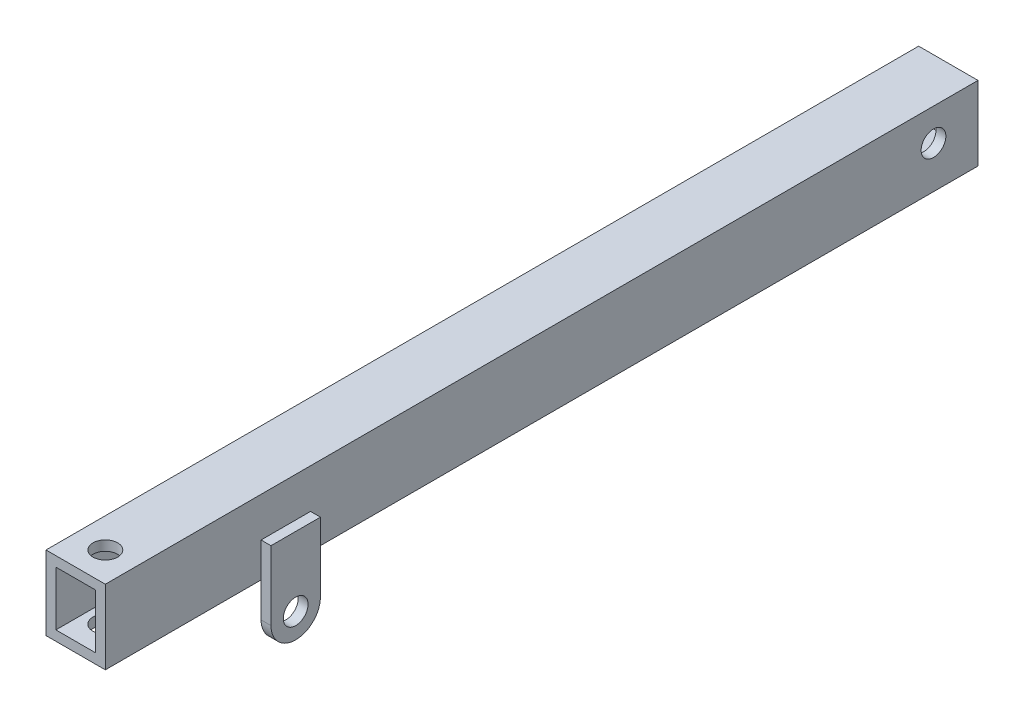
SolidWorks part; units mm, degrees
ref_plane "Alzado" through (0, 0, 0) normal (0, 0, 1) x (1, 0, 0)
ref_plane "Planta" through (0, 0, 0) normal (0, 1, 0) x (1, 0, 0)
ref_plane "Vista lateral" through (0, 0, 0) normal (1, 0, 0) x (0, 0, -1)
sketch "Croquis1" plane through (0, 0, 0) normal (0, 0, 1) x (1, 0, 0)
  line L1 (-6, -7.5) -> (6, -7.5)
  line L2 (-6, -7.5) -> (-6, 7.5)
  line L3 (-6, 7.5) -> (6, 7.5)
  line L4 (6, -7.5) -> (6, 7.5)
  line L5 (-6, -7.5) -> (6, 7.5) construction
  line L6 (-6, 7.5) -> (6, -7.5) construction
  line L7 (-4, -5.5) -> (4, -5.5)
  line L8 (-4, -5.5) -> (-4, 5.5)
  line L9 (-4, 5.5) -> (4, 5.5)
  line L10 (4, -5.5) -> (4, 5.5)
  line L11 (-4, -5.5) -> (4, 5.5) construction
  line L12 (-4, 5.5) -> (4, -5.5) construction
  point P0 (0, 0)
  point P6 (0, 0)
  dimension "D1" = 12
  dimension "D2" = 15
  dimension "D3" = 2
  dimension "D4" = 2
extrude "Saliente-Extruir1" add sketch "Croquis1" along normal mid plane 353
sketch "Croquis3" plane through (-6, 0, 0) normal (-1, 0, 0) x (0, 0, 1)
  line L0 (176.5, -7.5) -> (-176.5, -7.5) construction
  line L2 (-145, -14.5) -> (-145, -0.5)
  line L3 (-145, -0.5) -> (-135, -0.5)
  line L4 (-135, -14.5) -> (-135, -0.5)
  line L5 (-145, -14.5) -> (-135, -0.5) construction
  line L6 (-145, -0.5) -> (-135, -14.5) construction
  arc A0 (-145, -14.5) -> (-135, -14.5) centre (-140, -14.5) ccw
  circle A1 centre (-140, -14.5) radius 2.5
  point P0 (-140, -7.5)
  dimension "D5" = 5
  dimension "D6" = 5
  dimension "D1" = 14
  dimension "D2" = 10
  dimension "D3" = 135
  dimension "D4" = 7
extrude "Saliente-Extruir2" add sketch "Croquis3" along normal blind 2
mirror "Simetría1" about plane through (0, 0, 0) normal (1, 0, 0) of "Saliente-Extruir2"
mirror "Simetría2" about plane through (0, 0, 0) normal (0, 0, 1) of "Simetría1", "Saliente-Extruir2"
sketch "Sketch1" plane through (0, 7.5, 0) normal (0, 1, 0) x (1, 0, 0)
  circle A0 centre (0, 170.5) radius 2.5
  circle A1 centre (0, -170.5) radius 2.5
extrude "Cut-Extrude1" cut sketch "Sketch1" against normal through all
sketch "Sketch6" plane through (-6, 0, 0) normal (-1, 0, 0) x (0, 0, 1)
  line L1 (-176.5, 7.5) -> (0, 7.5)
  line L2 (-176.5, 7.5) -> (-176.5, -23.1225)
  line L3 (-176.5, -23.1225) -> (0, -23.1225)
  line L4 (0, 7.5) -> (0, -23.1225)
  dimension "D1" = 176.5
extrude "Cut-Extrude2" cut sketch "Sketch6" against normal through all
sketch "Sketch7" plane through (-8, 0, 0) normal (-1, 0, 0) x (0, 0, 1)
  line L1 (-145, -0.5) -> (-135, -0.5)
  line L2 (-145, -0.5) -> (-145, -20.5733)
  line L3 (-145, -20.5733) -> (-135, -20.5733)
  line L4 (-135, -0.5) -> (-135, -20.5733)
extrude "Cut-Extrude3" cut sketch "Sketch7" against normal blind 10
sketch "Sketch8" plane through (6, 0, 0) normal (1, 0, 0) x (0, 0, -1)
  line L0 (-135, -7.5) -> (0, -7.5) construction
  line L1 (0, 7.5) -> (-14, 7.5) construction
  line L2 (0, 7.5) -> (0, -7.5) construction
  line L3 (0, -7.5) -> (-14, -7.5) construction
  line L4 (-14, 7.5) -> (-14, -7.5) construction
  circle A0 centre (-9, 1) radius 2.5
  dimension "D4" = 5
  dimension "D1" = 14
  dimension "D2" = 5
  dimension "D3" = 6.5
extrude "Cut-Extrude4" cut sketch "Sketch8" against normal through all
